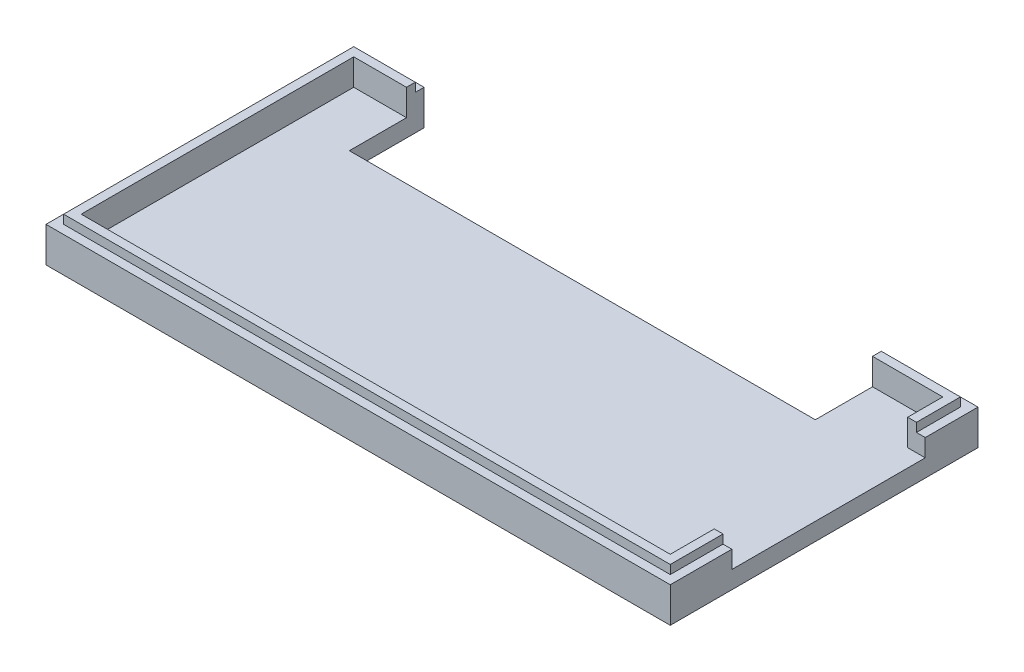
SolidWorks part; units mm, degrees
ref_plane "Front Plane" through (0, 0, 0) normal (0, 0, 1) x (1, 0, 0)
ref_plane "Top Plane" through (0, 0, 0) normal (0, 1, 0) x (1, 0, 0)
ref_plane "Right Plane" through (0, 0, 0) normal (1, 0, 0) x (0, 0, -1)
sketch "Sketch1" plane through (0, 0, 0) normal (0, 1, 0) x (1, 0, 0)
  line L4 (69, 33) -> (-2, 33)
  line L5 (-2, 33) -> (-2, -2)
  line L6 (-2, -2) -> (69, -2)
  line L7 (69, -2) -> (69, 33)
  dimension "D1" = 71
  dimension "D2" = 35
extrude "Boss-Extrude1" add sketch "Sketch1" along normal blind 2
sketch "Sketch2" plane through (0, 2, 0) normal (0, 1, 0) x (1, 0, 0)
  line L0 (67, 31) -> (0, 31)
  line L1 (0, 31) -> (0, 0)
  line L2 (0, 0) -> (67, 0)
  line L3 (67, 0) -> (67, 31)
  line L4 (69, -2) -> (69, 33)
  line L5 (69, 33) -> (-2, 33)
  line L6 (-2, 33) -> (-2, -2)
  line L7 (-2, -2) -> (69, -2)
  line L8 (69, -2) -> (69, 33)
  line L9 (69, 33) -> (-2, 33)
  line L10 (-2, 33) -> (-2, -2)
  line L11 (-2, -2) -> (69, -2)
  dimension "D1" = 0
  dimension "D2" = 2
extrude "Boss-Extrude2" add sketch "Sketch2" along normal blind 2
sketch "Sketch3" plane through (0, 4, 0) normal (0, 1, 0) x (1, 0, 0)
  line L0 (67, 31) -> (0, 31) construction
  line L1 (0, 31) -> (0, 0) construction
  line L2 (0, 0) -> (67, 0) construction
  line L3 (67, 0) -> (67, 31) construction
  line L4 (67, 31) -> (0, 31)
  line L5 (0, 31) -> (0, 0)
  line L6 (0, 0) -> (67, 0)
  line L7 (67, 0) -> (67, 31)
  line L8 (68, 32) -> (-1, 32)
  line L9 (-1, 32) -> (-1, -1)
  line L10 (-1, -1) -> (68, -1)
  line L11 (68, -1) -> (68, 32)
  dimension "D1" = 1
extrude "Boss-Extrude3" add sketch "Sketch3" along normal blind 1
sketch "Sketch4" plane through (67, 0, 0) normal (-1, 0, 0) x (0, 0, 1)
  line L0 (-27, 5) -> (-27, 2)
  line L1 (0, 5) -> (-31, 5) construction
  line L2 (0, 2) -> (-31, 2) construction
  line L3 (-27, 2) -> (-5, 2)
  line L4 (-5, 2) -> (-5, 5)
  line L5 (-32, 5) -> (1, 5) construction
  line L6 (-5, 5) -> (-27, 5)
  line L7 (-31, 5) -> (-31, 2) construction
  line L8 (0, 5) -> (0, 2) construction
  dimension "D1" = 4
  dimension "D2" = 5
extrude "Cut-Extrude1" cut sketch "Sketch4" against normal blind 5
sketch "Sketch5" plane through (0, 0, 0) normal (0, -1, 0) x (1, 0, 0)
  line L0 (59, -33) -> (59, -24.5)
  line L1 (69, -33) -> (-2, -33) construction
  line L2 (59, -24.5) -> (6, -24.5)
  line L3 (6, -24.5) -> (6, -33)
  line L4 (6, -33) -> (59, -33)
  line L5 (69, 2) -> (69, -33) construction
  line L6 (-2, -33) -> (-2, 2) construction
  dimension "D1" = 10
  dimension "D2" = 8
  dimension "D3" = 8.5
extrude "Cut-Extrude2" cut sketch "Sketch5" against normal blind 5
